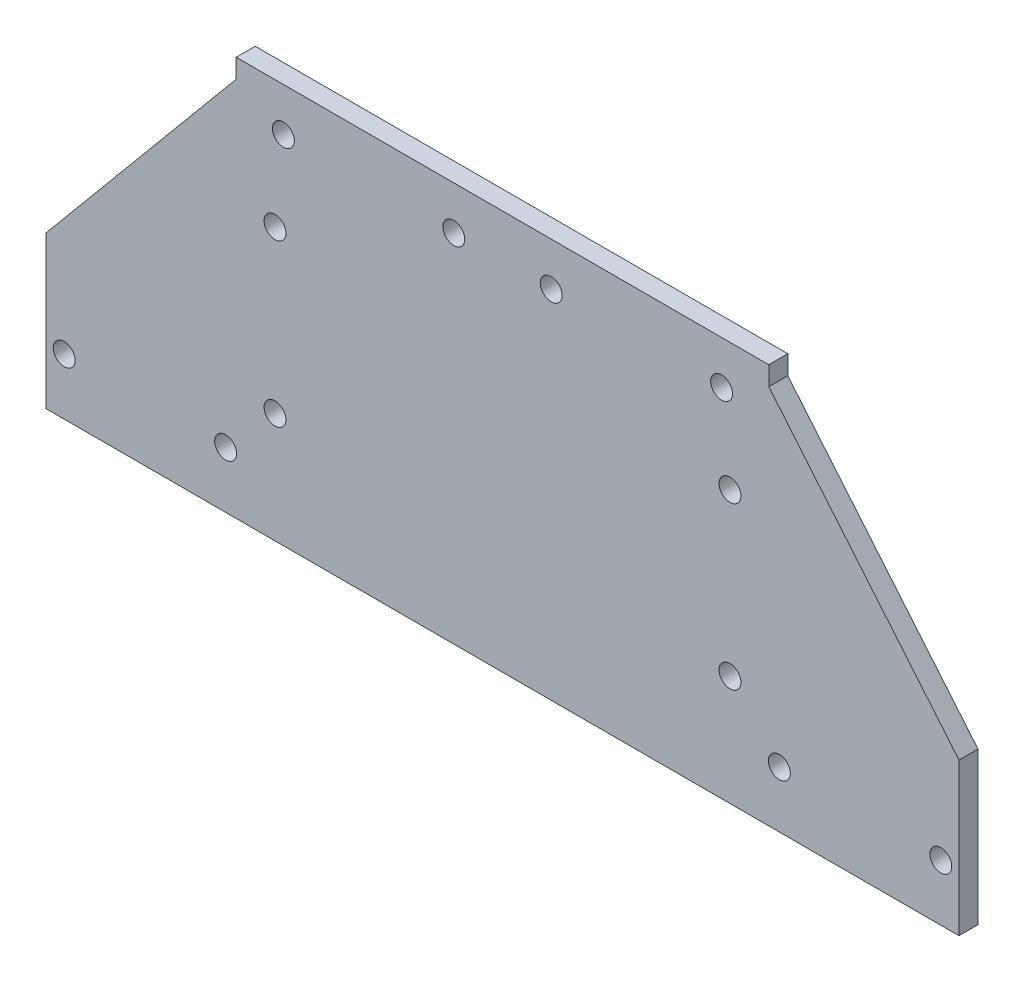
SolidWorks part; units mm, degrees
ref_plane "Front" through (0, 0, 0) normal (0, 0, 1) x (1, 0, 0)
ref_plane "Top" through (0, 0, 0) normal (0, 1, 0) x (1, 0, 0)
ref_plane "Right" through (0, 0, 0) normal (1, 0, 0) x (0, 0, -1)
sketch "Sketch1" plane through (0, 0, 0) normal (0, 1, 0) x (1, 0, 0)
  line L1 (44.45, -1.5875) -> (-44.45, -1.5875)
  line L2 (44.45, -1.5875) -> (44.45, 1.5875)
  line L3 (44.45, 1.5875) -> (-44.45, 1.5875)
  line L4 (-44.45, -1.5875) -> (-44.45, 1.5875)
  line L5 (44.45, -1.5875) -> (-44.45, 1.5875) construction
  line L6 (44.45, 1.5875) -> (-44.45, -1.5875) construction
  point P0 (0, 0)
  dimension "D1" = 3.175
  dimension "D2" = 88.9
extrude "Boss-Extrude1" add sketch "Sketch1" along normal blind 51.435
sketch "Sketch2" plane through (0, 0, 1.5875) normal (0, 0, 1) x (1, 0, 0)
  line L0 (-44.45, 51.435) -> (-36.576, 51.435) construction
  line L1 (-44.45, 51.435) -> (44.45, 51.435) construction
  line L2 (-36.576, 51.435) -> (-36.576, 44.196) construction
  line L3 (0, 51.435) -> (0, 0) construction
  line L4 (0, 51.435) -> (-8.128, 51.435) construction
  line L5 (-8.128, 51.435) -> (-8.128, 44.196) construction
  circle A0 centre (-36.576, 44.196) radius 1.8288
  circle A1 centre (-8.128, 44.196) radius 1.8288
  circle A2 centre (8.128, 44.196) radius 1.8288
  circle A3 centre (36.576, 44.196) radius 1.8288
  dimension "D5" = 3.6576
  dimension "D6" = 3.6576
  dimension "D1" = 7.239
  dimension "D2" = 7.239
  dimension "D3" = 8.128
  dimension "D4" = 7.874
extrude "Cut-Extrude1" cut sketch "Sketch2" against normal through all
sketch "Sketch3" plane through (0, 0, 1.5875) normal (0, 0, 1) x (1, 0, 0)
  line L0 (0, 51.435) -> (0, 0) construction
  line L1 (-44.45, 51.435) -> (44.45, 51.435) construction
  line L2 (-44.45, 0) -> (-31.496, 0) construction
  line L3 (-44.45, 0) -> (44.45, 0) construction
  line L4 (-37.973, 0) -> (-37.973, 3.175) construction
  line L5 (-37.973, 3.175) -> (-37.973, 30.1244) construction
  circle A0 centre (-37.973, 3.175) radius 1.8288
  circle A1 centre (-37.973, 30.1244) radius 1.8288
  circle A2 centre (37.973, 3.175) radius 1.8288
  circle A3 centre (37.973, 30.1244) radius 1.8288
  dimension "D3" = 3.6576
  dimension "D5" = 3.6576
  dimension "D1" = 12.954
  dimension "D2" = 3.175
  dimension "D4" = 26.9494
extrude "Cut-Extrude2" cut sketch "Sketch3" against normal through all
sketch "Sketch4" plane through (0, 0, 1.5875) normal (0, 0, 1) x (1, 0, 0)
  line L0 (-44.45, 51.435) -> (44.45, 51.435) construction
  line L1 (0, 51.435) -> (0, 0) construction
  line L2 (-44.45, 0) -> (-44.45, 48.26)
  line L3 (-44.45, 48.26) -> (-76.2, 48.26)
  line L4 (-76.2, 0) -> (-76.2, 48.26)
  line L5 (76.2, 0) -> (76.2, -15.24)
  line L6 (0, 0) -> (-44.45, 0)
  line L8 (76.2, -15.24) -> (-76.2, -15.24)
  line L9 (-76.2, 0) -> (-76.2, -15.24)
  line L10 (76.2, 0) -> (76.2, 48.26)
  line L11 (44.45, 48.26) -> (76.2, 48.26)
  line L12 (0, -15.24) -> (0, -29.2522) construction
  line L13 (0, 0) -> (44.45, 0)
  line L14 (44.45, 0) -> (44.45, 48.26)
  dimension "D1" = 31.75
  dimension "D2" = 3.175
  dimension "D3" = 15.24
extrude "Boss-Extrude2" add sketch "Sketch4" against normal blind 3.175
sketch "Sketch5" plane through (0, 0, 1.5875) normal (0, 0, 1) x (1, 0, 0)
  line L0 (-76.2, -15.24) -> (-76.2, 10.16) construction
  line L1 (-76.2, 48.26) -> (-76.2, -15.24) construction
  line L2 (-44.45, 48.26) -> (-76.2, 10.16)
  line L3 (-76.2, 10.16) -> (-76.2, -15.24)
  line L4 (-76.2, 10.16) -> (-76.2, 48.26)
  line L5 (-76.2, 48.26) -> (-44.45, 48.26)
  line L6 (0, 51.435) -> (0, -15.24) construction
  line L7 (-44.45, 51.435) -> (44.45, 51.435) construction
  line L8 (-76.2, -15.24) -> (76.2, -15.24) construction
  line L9 (76.2, 10.16) -> (76.2, 48.26)
  line L10 (76.2, 48.26) -> (44.45, 48.26)
  line L11 (44.45, 48.26) -> (76.2, 10.16)
  line M2 (-44.45, 48.26) -> (-76.2, 48.26)
  line M3 (-76.2, 48.26) -> (-76.2, -15.24)
  line M5 (76.2, -15.24) -> (76.2, 48.26)
  line M6 (76.2, 48.26) -> (44.45, 48.26)
  dimension "D1" = 25.4
extrude "Cut-Extrude3" cut sketch "Sketch5" against normal through all contours L2 M2 M3 | L11 M6 M5
sketch "Sketch6" plane through (0, 0, 1.5875) normal (0, 0, 1) x (1, 0, 0)
  line L0 (-76.2, -15.24) -> (-73.1647, -15.24) construction
  line L1 (-76.2, -15.24) -> (76.2, -15.24) construction
  line L2 (-73.1647, -15.24) -> (-73.1647, -5.842) construction
  line L3 (0, 51.435) -> (0, -15.24) construction
  line L4 (-44.45, 51.435) -> (44.45, 51.435) construction
  line L5 (-73.1647, -5.842) -> (-46.2153, -5.842) construction
  circle A0 centre (-73.1647, -5.842) radius 1.8288
  circle A1 centre (-46.2153, -5.842) radius 1.8288
  circle A2 centre (46.2153, -5.842) radius 1.8288
  circle A3 centre (73.1647, -5.842) radius 1.8288
  dimension "D4" = 3.6576
  dimension "D5" = 3.6576
  dimension "D1" = 3.0353
  dimension "D2" = 9.398
  dimension "D3" = 26.9494
extrude "Cut-Extrude4" cut sketch "Sketch6" against normal through all
